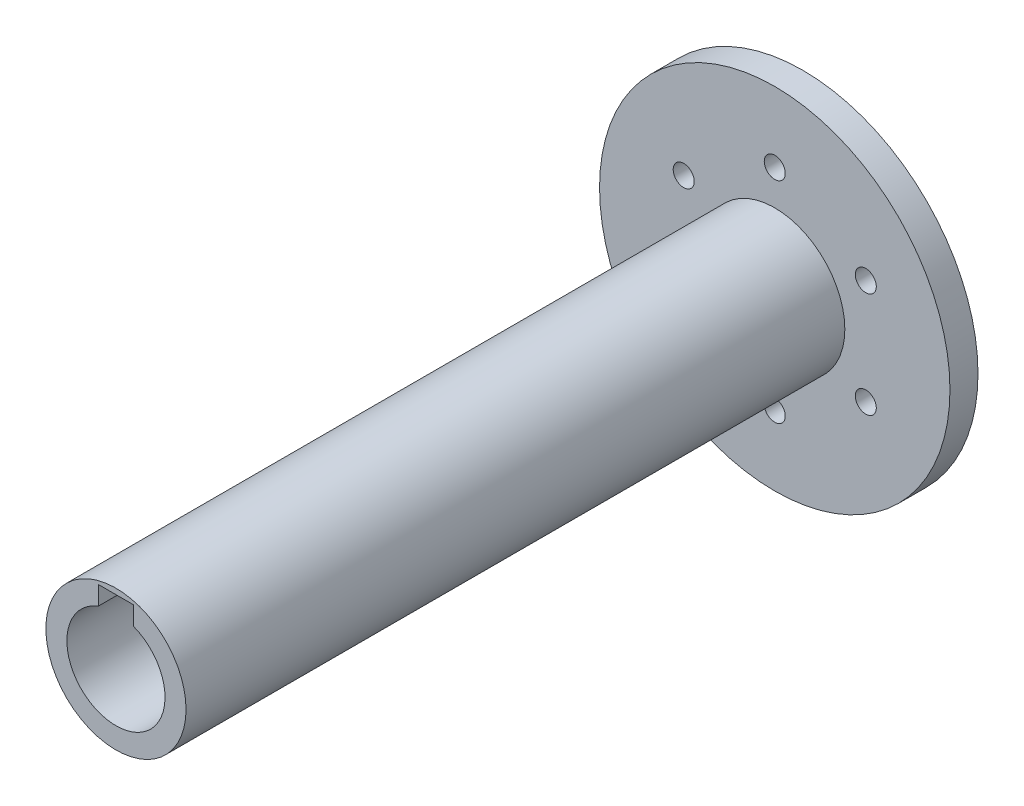
SolidWorks part; units mm, degrees
ref_plane "前视基准面" through (0, 0, 0) normal (0, 0, 1) x (1, 0, 0)
ref_plane "上视基准面" through (0, 0, 0) normal (0, 1, 0) x (1, 0, 0)
ref_plane "右视基准面" through (0, 0, 0) normal (1, 0, 0) x (0, 0, -1)
sketch "草图1" plane through (0, 0, 0) normal (0, 0, 1) x (1, 0, 0)
  circle A0 centre (0, 0) radius 10
  dimension "D1" = 20
extrude "凸台-拉伸1" add sketch "草图1" along normal blind 94
sketch "草图2" plane through (0, 0, 94) normal (0, 0, 1) x (1, 0, 0)
  line L2 (-2.5, 6.5383) -> (-2.5, 9.2)
  line L3 (-2.5, 9.2) -> (2.5, 9.2)
  line L4 (2.5, 6.5383) -> (2.5, 9.2)
  line L5 (2.1086, 7.8433) -> (2.5, 9.2) construction
  line L6 (-2.5, 9.2) -> (-2.1086, 7.8433) construction
  arc A0 (-2.5, 6.5383) -> (2.5, 6.5383) centre (0, 0) ccw
  point P1 (0, 9.2)
  dimension "D1" = 14
  dimension "D2" = 5
  dimension "D3" = 9.2
extrude "切除-拉伸1" cut sketch "草图2" against normal blind 30
sketch "草图3" plane through (0, 0, 0) normal (0, 0, -1) x (-1, 0, 0)
  circle A0 centre (0, 0) radius 1.5
  dimension "D1" = 3
extrude "切除-拉伸2" cut sketch "草图3" against normal through all
sketch "草图4" plane through (0, 0, 0) normal (0, 0, -1) x (-1, 0, 0)
  circle A0 centre (0, 0) radius 25
  circle A1 centre (0, 0) radius 1.5
  dimension "D1" = 50
extrude "凸台-拉伸2" add sketch "草图4" along normal blind 4
sketch "草图5" plane through (0, 0, -4) normal (0, 0, -1) x (-1, 0, 0)
  line L0 (0, 25) -> (0, -25) construction
  circle A0 centre (0, 0) radius 25 construction
  circle A1 centre (0, 15) radius 1.5
  circle A2 centre (12.9904, 7.5) radius 1.5
  circle A3 centre (12.9904, -7.5) radius 1.5
  circle A4 centre (0, -15) radius 1.5
  circle A5 centre (-12.9904, -7.5) radius 1.5
  circle A6 centre (-12.9904, 7.5) radius 1.5
  point P21 (0, 0)
  dimension "D1" = 3
  dimension "D2" = 15
  dimension "D3" = 6
extrude "切除-拉伸5" cut sketch "草图5" against normal blind 4 contours A5 | L0 A4 | A4 L0 | A3 | A2 | A1 | A6
